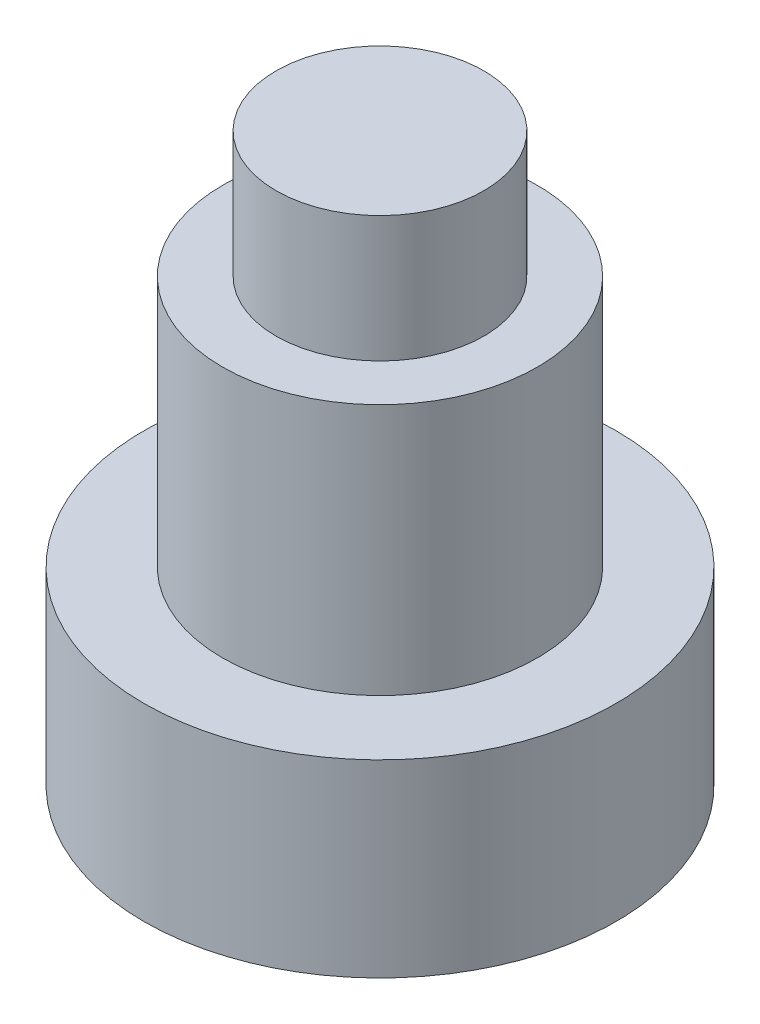
SolidWorks part; units mm, degrees
ref_plane "Front Plane" through (0, 0, 0) normal (0, 0, 1) x (1, 0, 0)
ref_plane "Top Plane" through (0, 0, 0) normal (0, 1, 0) x (1, 0, 0)
ref_plane "Right Plane" through (0, 0, 0) normal (1, 0, 0) x (0, 0, -1)
sketch "Sketch1" plane through (0, 0, 0) normal (0, 1, 0) x (1, 0, 0)
  circle A0 centre (0, 0) radius 3.75
extrude "Boss-Extrude1" add sketch "Sketch1" along normal blind 7
sketch "Sketch2" plane through (0, 7, 0) normal (0, 1, 0) x (1, 0, 0)
  circle A0 centre (0, 0) radius 2.5
  circle A1 centre (0, 0) radius 3.75
extrude "Cut-Extrude1" cut sketch "Sketch2" against normal blind 4
sketch "Sketch3" plane through (0, 7, 0) normal (0, 1, 0) x (1, 0, 0)
  circle A0 centre (0, 0) radius 1.65
extrude "Boss-Extrude2" add sketch "Sketch3" along normal blind 2
